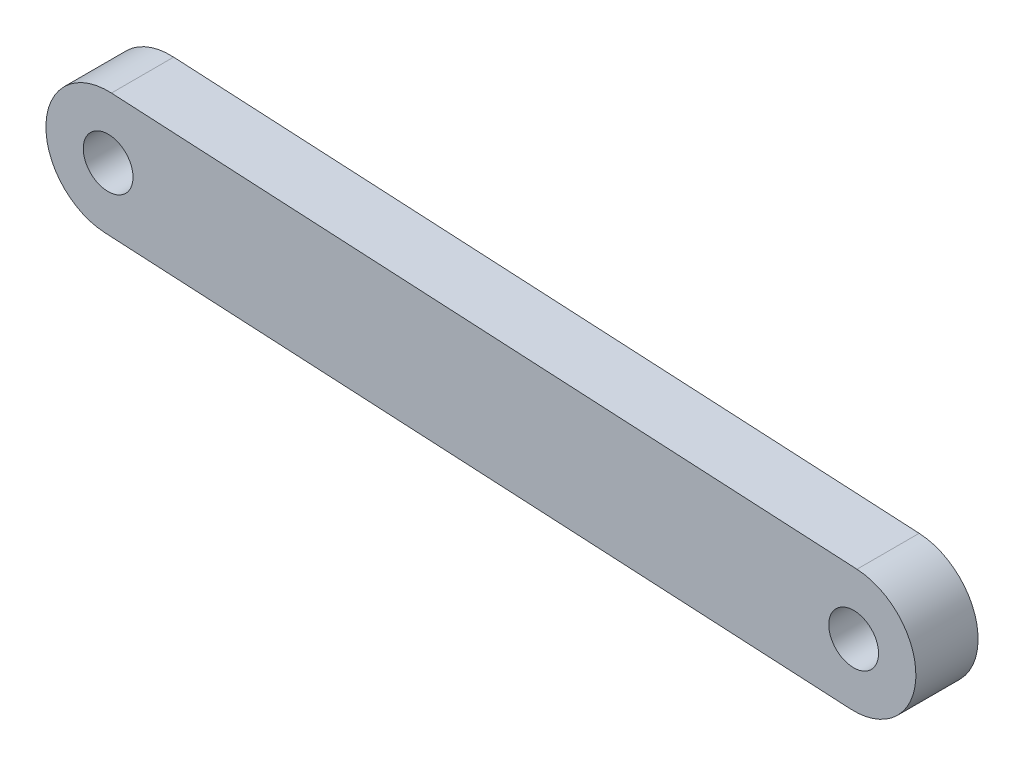
SolidWorks part; units mm, degrees
ref_plane "Front Plane" through (0, 0, 0) normal (0, 0, 1) x (1, 0, 0)
ref_plane "Top Plane" through (0, 0, 0) normal (0, 1, 0) x (1, 0, 0)
ref_plane "Right Plane" through (0, 0, 0) normal (1, 0, 0) x (0, 0, -1)
sketch "Sketch1" plane through (0, 0, 0) normal (0, 0, 1) x (0.4312, 0.9023, 0)
  line L0 (-23.2742, 28.2643) -> (-18.6548, 30.1777) construction
  line L1 (-18.6548, 30.1777) -> (-27.8936, 26.3509) construction
  line L2 (-18.6548, 30.1777) -> (-41.6158, 85.6105)
  line L3 (-27.8936, 26.3509) -> (-50.8546, 81.7837)
  line L4 (-41.6158, 85.6105) -> (-50.8546, 81.7837) construction
  circle A0 centre (-23.2742, 28.2643) radius 2
  arc A1 (-27.8936, 26.3509) -> (-18.6548, 30.1777) centre (-23.2742, 28.2643) ccw
  arc A2 (-50.8546, 81.7837) -> (-41.6158, 85.6105) centre (-46.2352, 83.6971) cw
  circle A3 centre (-46.2352, 83.6971) radius 2
  dimension "D1" = 10
  dimension "D3" = 5
  dimension "D4" = 4
  dimension "D5" = 4
  dimension "D6" = 5
  dimension "D2" = 60
extrude "Boss-Extrude1" add sketch "Sketch1" along normal blind 5
move or copy body "Body-Move/Copy1" [suppressed] bodies to move or copy 101
